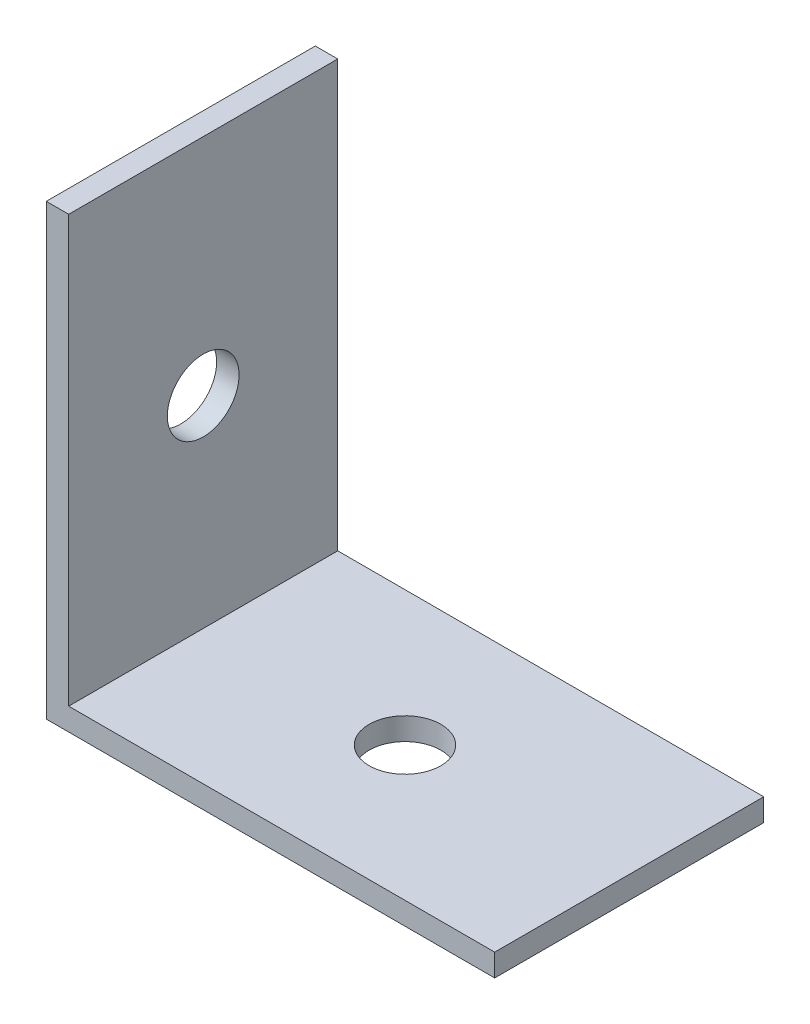
SolidWorks part; units mm, degrees
ref_plane "Front Plane" through (0, 0, 0) normal (0, 0, 1) x (1, 0, 0)
ref_plane "Top Plane" through (0, 0, 0) normal (0, 1, 0) x (1, 0, 0)
ref_plane "Right Plane" through (0, 0, 0) normal (1, 0, 0) x (0, 0, -1)
sketch "Sketch1" plane through (0, 0, 0) normal (0, 0, 1) x (1, 0, 0)
  line L0 (0, 0) -> (20, 0)
  line L1 (20, 0) -> (20, 1)
  line L2 (20, 1) -> (1, 1)
  line L3 (1, 1) -> (1, 20)
  line L4 (1, 20) -> (0, 20)
  line L5 (0, 20) -> (0, 0)
  dimension "D1" = 20
  dimension "D2" = 1
extrude "Boss-Extrude1" add sketch "Sketch1" along normal blind 12
sketch "Sketch2" plane through (0, 0, 0) normal (0, -1, 0) x (1, 0, 0)
  line L0 (20, 6) -> (0, 6) construction
  line L1 (20, 12) -> (20, 0) construction
  line L2 (0, 12) -> (0, 0) construction
  circle A0 centre (10, 6) radius 1.6
  dimension "D1" = 3.2
  dimension "D2" = 10
extrude "Cut-Extrude1" cut sketch "Sketch2" against normal through all
sketch "Sketch3" plane through (0, 0, 0) normal (-1, 0, 0) x (0, 0, 1)
  line L0 (6, 20) -> (6, 0) construction
  line L1 (12, 20) -> (0, 20) construction
  line L2 (12, 0) -> (0, 0) construction
  circle A0 centre (6, 10) radius 1.6
  dimension "D1" = 3.2
extrude "Cut-Extrude2" cut sketch "Sketch3" against normal through all
sketch "Sketch4" plane through (0, 0, 0) normal (-1, 0, 0) x (0, 0, 1)
  line L0 (6, 20) -> (6, 0) construction
  line L1 (12, 20) -> (0, 20) construction
  line L2 (12, 0) -> (0, 0) construction
